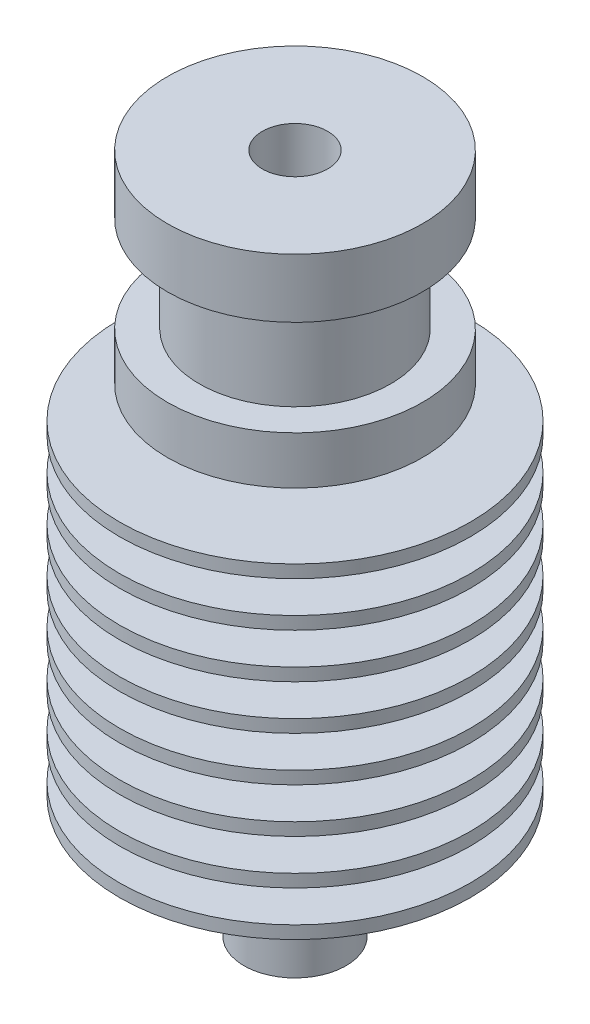
SolidWorks part; units mm, degrees
material "Alloy Steel"
ref_plane "Front Plane" through (0, 0, 0) normal (0, 0, 1) x (1, 0, 0)
ref_plane "Top Plane" through (0, 0, 0) normal (0, 1, 0) x (1, 0, 0)
ref_plane "Right Plane" through (0, 0, 0) normal (1, 0, 0) x (0, 0, -1)
sketch "Sketch1" plane through (0, 0, 0) normal (0, 0, 1) x (1, 0, 0)
  line L0 (0, -21.35) -> (0, 21.35) construction
  line L1 (2.05, 21.35) -> (8, 21.35)
  line L2 (2.05, -21.35) -> (3.2, -21.35)
  line L3 (8, 21.35) -> (8, 17.65)
  line L4 (8, 17.65) -> (6, 17.65)
  line L5 (6, 17.65) -> (6, 11.65)
  line L6 (6, 11.65) -> (8, 11.65)
  line L7 (8, 11.65) -> (8, 8.65)
  line L8 (8, 8.65) -> (3, 8.65)
  line L9 (3, 8.65) -> (3, 6.65)
  line L10 (3, 6.65) -> (11, 6.65)
  line L11 (2.05, 21.35) -> (2.05, -21.35)
  line L12 (11, 6.65) -> (11, 5.85)
  line L13 (11, 5.85) -> (3, 5.85)
  line L14 (3, 5.85) -> (3, 3.85)
  line L15 (3, 3.85) -> (11, 3.85)
  line L16 (11, 3.85) -> (11, 3.05)
  line L17 (11, 3.05) -> (3, 3.05)
  line L18 (3, 3.05) -> (3, 1.05)
  line L19 (3, 1.05) -> (11, 1.05)
  line L20 (11, 1.05) -> (11, 0.25)
  line L21 (11, 0.25) -> (3, 0.25)
  line L22 (3, 0.25) -> (3, -1.75)
  line L23 (3, -1.75) -> (11, -1.75)
  line L24 (11, -1.75) -> (11, -2.55)
  line L25 (11, -2.55) -> (3, -2.55)
  line L26 (3, -2.55) -> (3, -4.55)
  line L27 (3, -4.55) -> (11, -4.55)
  line L28 (11, -4.55) -> (11, -5.35)
  line L29 (11, -5.35) -> (3, -5.35)
  line L30 (3, -5.35) -> (3, -7.35)
  line L31 (3, -7.35) -> (11, -7.35)
  line L32 (11, -7.35) -> (11, -8.15)
  line L33 (11, -8.15) -> (3, -8.15)
  line L34 (3, -8.15) -> (3, -10.15)
  line L35 (3, -10.15) -> (11, -10.15)
  line L36 (11, -10.15) -> (11, -10.95)
  line L37 (11, -10.95) -> (3, -10.95)
  line L38 (3, -10.95) -> (3, -12.95)
  line L39 (3, -12.95) -> (11, -12.95)
  line L40 (11, -12.95) -> (11, -13.75)
  line L41 (11, -13.75) -> (3.2, -13.75)
  line L42 (3.2, -21.35) -> (3.2, -16.35)
  line L43 (3.2, -16.35) -> (2.8131, -16.35)
  line L44 (2.8131, -16.35) -> (2.8131, -13.75)
  line L45 (2.8131, -13.75) -> (3.2, -13.75)
  dimension "D1" = 42.7
  dimension "D2" = 8
  dimension "D3" = 11
  dimension "D4" = 3.7
  dimension "D5" = 6
  dimension "D6" = 3
  dimension "D7" = 6
  dimension "D8" = 4.1
  dimension "D9" = 3
  dimension "D11" = 0.8
  dimension "D12" = 2
  dimension "D13" = 5
  dimension "D14" = 3.2
revolve "Revolve1" add sketch "Sketch1" angle 360 about L0
